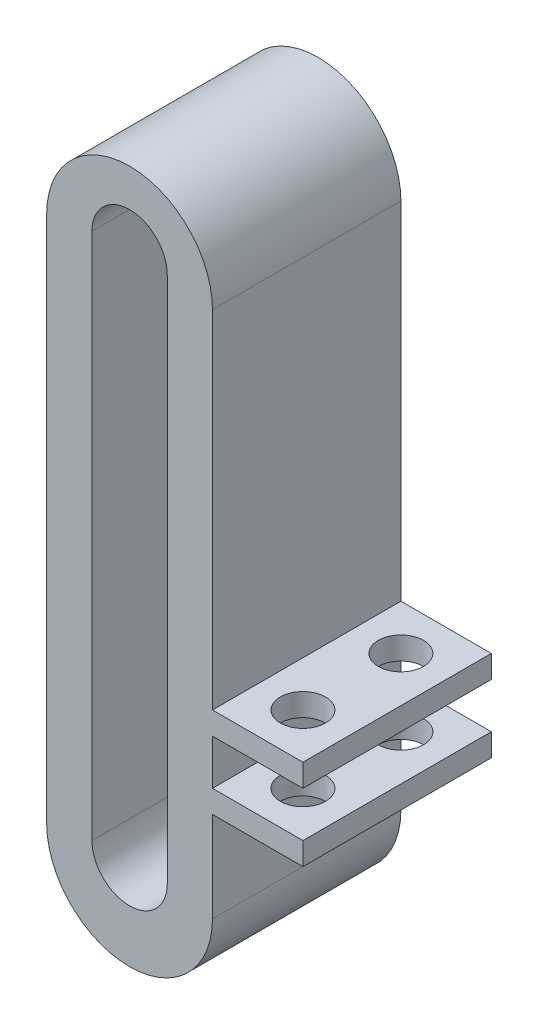
SolidWorks part; units mm, degrees
ref_plane "Front Plane" through (0, 0, 0) normal (0, 0, 1) x (1, 0, 0)
ref_plane "Top Plane" through (0, 0, 0) normal (0, 1, 0) x (1, 0, 0)
ref_plane "Right Plane" through (0, 0, 0) normal (1, 0, 0) x (0, 0, -1)
sketch "Sketch1" plane through (0, 0, 0) normal (0, 0, 1) x (1, 0, 0)
  line L0 (0, 17.5) -> (0, -17.5) construction
  line L1 (2.5, 17.5) -> (2.5, -17.5)
  line L2 (-2.5, 17.5) -> (-2.5, -17.5)
  line L3 (5.5, 17) -> (5.5, -18)
  line L4 (-5.5, 17) -> (-5.5, -18)
  arc A0 (2.5, 17.5) -> (-2.5, 17.5) centre (0, 17.5) ccw
  arc A1 (-2.5, -17.5) -> (2.5, -17.5) centre (0, -17.5) ccw
  arc A2 (-5.5, -18) -> (5.5, -18) centre (0, -18) ccw
  arc A3 (5.5, 17) -> (-5.5, 17) centre (0, 17) ccw
  point P2 (0, 0)
  dimension "D4" = 35
  dimension "D7" = 5.5
  dimension "D8" = 5.5
  dimension "D1" = 3
  dimension "D2" = 3
  dimension "D3" = 2.5
  dimension "D5" = 35
  dimension "D6" = 17
extrude "Boss-Extrude1" add sketch "Sketch1" along normal blind 12.5
sketch "Sketch2" plane through (5.5, 0, 0) normal (1, 0, 0) x (0, 0, -1)
  line L0 (-12.5, -18) -> (-12.5, 17) construction
  line L5 (0, -18) -> (0, 17) construction
  line L6 (-12.5, 17) -> (0, 17) construction
  line L9 (-12.5, -12) -> (0, -12)
  line L10 (-12.5, -12) -> (-12.5, -10.5)
  line L11 (-12.5, -10.5) -> (0, -10.5)
  line L12 (0, -12) -> (0, -10.5)
  line L13 (-12.5, -6) -> (0, -6)
  line L14 (-12.5, -6) -> (-12.5, -7.5)
  line L15 (-12.5, -7.5) -> (0, -7.5)
  line L16 (0, -6) -> (0, -7.5)
  dimension "D1" = 23
  dimension "D2" = 3
  dimension "D3" = 1.5
  dimension "D4" = 1.5
extrude "Boss-Extrude2" add sketch "Sketch2" along normal blind 6
sketch "Sketch3" plane through (0, -10.5, 0) normal (0, 1, 0) x (1, 0, 0)
  line L0 (11.5, 0) -> (5.5, 0) construction
  line L1 (5.5, -6.25) -> (11.5, -6.25) construction
  line L2 (5.5, 0) -> (5.5, -12.5) construction
  line L3 (11.5, 0) -> (11.5, -12.5) construction
  circle A1 centre (8.5, -3) radius 1.5
  circle A2 centre (8.5, -9.5) radius 1.5
  point P10 (8.5, -9.5)
  dimension "D1" = 3
  dimension "D2" = 3
  dimension "D3" = 3
extrude "Cut-Extrude1" cut sketch "Sketch3" against normal through all both and the other way through all
sketch "Sketch5" plane through (0, 0, 0) normal (0, 1, 0) x (1, 0, 0)
  line L1 (-0.5, -3.75) -> (0.5, -3.75)
  line L2 (-0.5, -3.75) -> (-0.5, -8.75)
  line L3 (-0.5, -8.75) -> (0.5, -8.75)
  line L4 (0.5, -3.75) -> (0.5, -8.75)
  line L5 (-5.5, -12.5) -> (-5.5, 0) construction
  line L6 (5.5, 0) -> (-5.5, 0) construction
  dimension "D1" = 5
  dimension "D2" = 1
  dimension "D3" = 5
  dimension "D4" = 3.75
extrude "Cut-Extrude2" cut sketch "Sketch5" against normal through all
